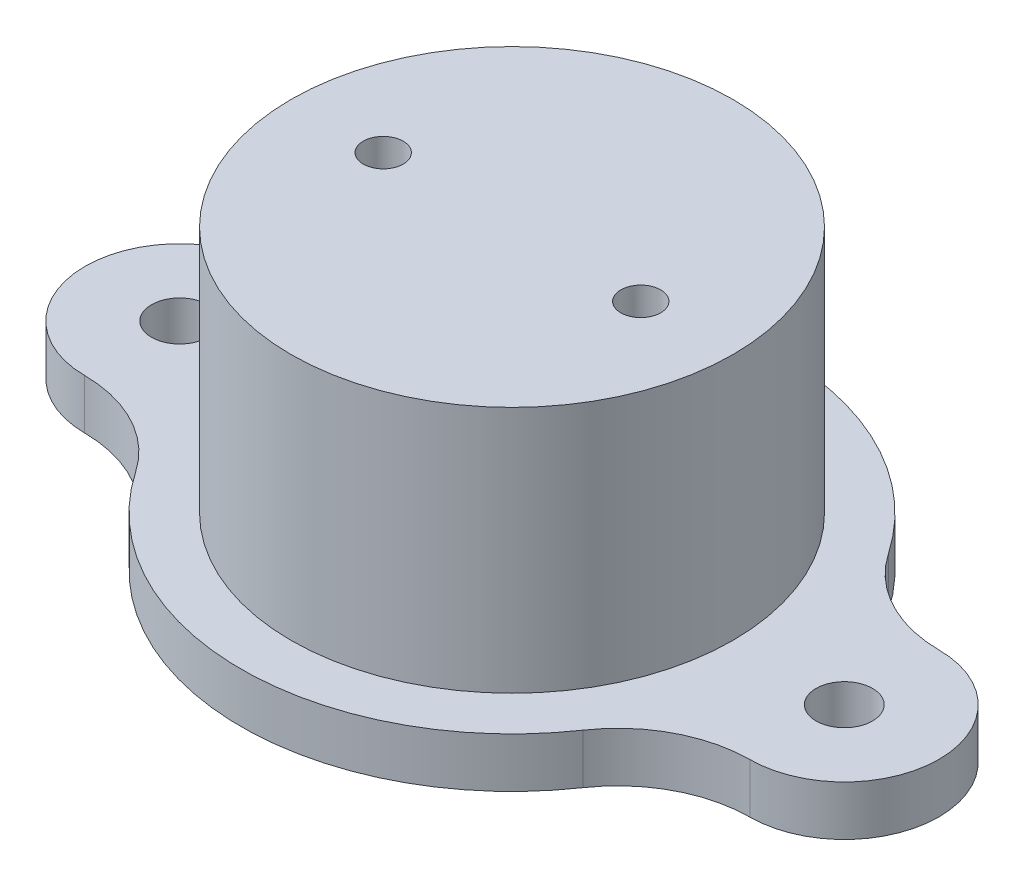
SolidWorks part; units mm, degrees
ref_plane "Front Plane" through (0, 0, 0) normal (0, 0, 1) x (1, 0, 0)
ref_plane "Top Plane" through (0, 0, 0) normal (0, 1, 0) x (1, 0, 0)
ref_plane "Right Plane" through (0, 0, 0) normal (1, 0, 0) x (0, 0, -1)
sketch "Sketch1" plane through (0, 0, 0) normal (0, 0, 1) x (1, 0, 0)
  line L0 (0, -272.3239) -> (0, 13343.8688) construction
  line L1 (0, 0) -> (0, 3)
  line L2 (0, 3) -> (13.3, 3)
  line L3 (13.3, 3) -> (13.3, -16)
  line L4 (13.3, -16) -> (11.7, -16)
  line L5 (11.7, -16) -> (11.7, 0)
  line L6 (11.7, 0) -> (0, 0)
  line L7 (13.3, -11.9) -> (16.3, -11.9)
  line L8 (16.3, -11.9) -> (16.3, -14.9)
  line L9 (16.3, -14.9) -> (13.3, -16)
  dimension "D1" = 3
  dimension "D2" = 23.4
  dimension "D3" = 16
  dimension "D4" = 26.6
  dimension "D5" = 14.9
  dimension "D6" = 3
  dimension "D7" = 3
revolve "Revolve1" add sketch "Sketch1" angle 360 about L0
sketch "Sketch3" plane through (0, -11.9, 0) normal (0, 1, 0) x (1, 0, 0)
  line L0 (0, -1000) -> (0, 49000) construction
  circle A0 centre (20, 0) radius 1.7
  circle A1 centre (-20, 0) radius 1.7
  arc A2 (-20.0291, 5.6999) -> (-20.0291, -5.6999) centre (-20, 0) ccw
  arc A3 (-20.0291, 5.6999) -> (-13.4626, 9.1896) centre (-20.07, 13.6998) ccw
  circle A4 centre (0, 0) radius 16.3 construction
  arc A5 (-13.4626, 9.1896) -> (-13.4626, -9.1896) centre (0, 0) ccw
  circle A6 centre (-20, 0) radius 5.7 construction
  arc A7 (-13.4626, -9.1896) -> (-20.0291, -5.6999) centre (-20.07, -13.6998) ccw
  arc A8 (13.4626, -9.1896) -> (13.4626, 9.1896) centre (0, 0) ccw
  arc A9 (13.4626, -9.1896) -> (20.0291, -5.6999) centre (20.07, -13.6998) cw
  arc A10 (20.0291, 5.6999) -> (13.4626, 9.1896) centre (20.07, 13.6998) cw
  arc A11 (20.0291, 5.6999) -> (20.0291, -5.6999) centre (20, 0) cw
  dimension "D1" = 3.4
  dimension "D4" = 16
  dimension "D2" = 40
  dimension "D3" = 4
extrude "Boss-Extrude4" add sketch "Sketch3" against normal blind 3
sketch "Sketch4" plane through (0, 0, 0) normal (0, 1, 0) x (1, 0, 0)
  line L0 (0, -1000) -> (0, 49000) construction
  circle A0 centre (7.75, 0) radius 1.2
  circle A1 centre (-7.75, 0) radius 1.2
  dimension "D1" = 2.4
  dimension "D2" = 15.5
extrude "Cut-Extrude3" cut sketch "Sketch4" along normal up to next contours A0 | A1
